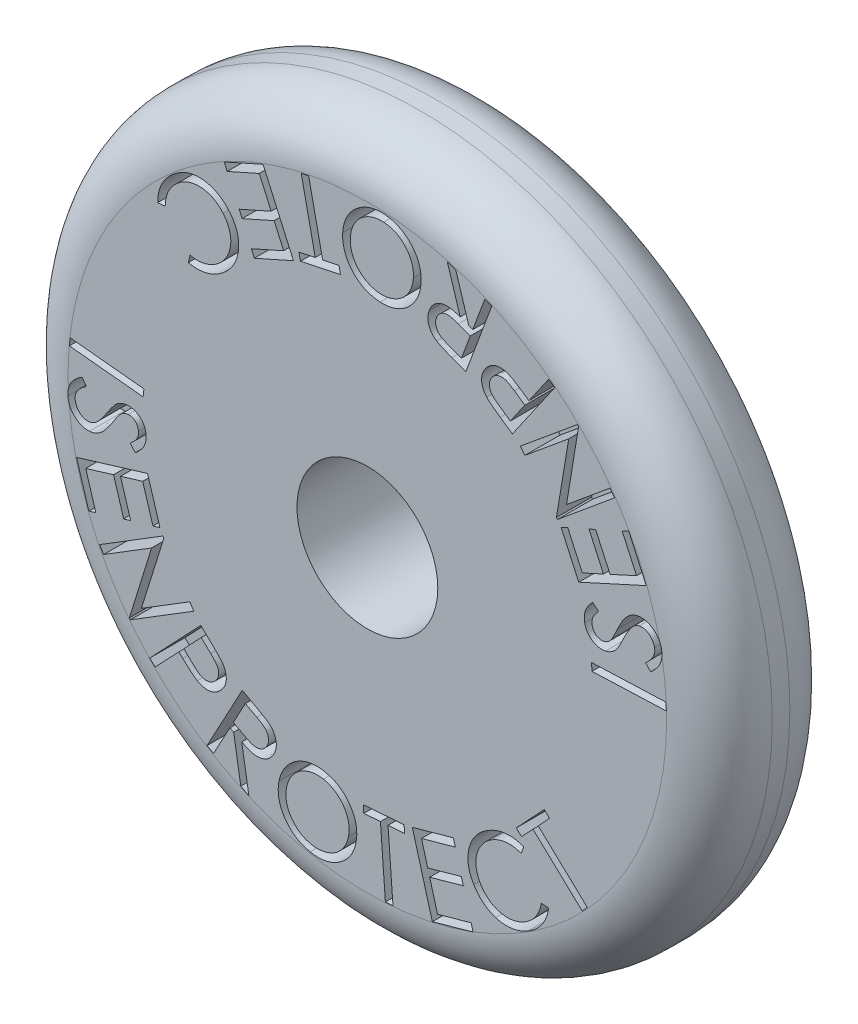
SolidWorks part; units mm, degrees
ref_plane "Plan de face" through (0, 0, 0) normal (0, 0, 1) x (1, 0, 0)
ref_plane "Plan de dessus" through (0, 0, 0) normal (0, 1, 0) x (1, 0, 0)
ref_plane "Plan de droite" through (0, 0, 0) normal (1, 0, 0) x (0, 0, -1)
sketch "Sketch1" plane through (0, 0, 0) normal (0, 0, 1) x (1, 0, 0)
  circle A0 centre (0, 0) radius 20
  dimension "D1" = 40
extrude "Boss-Extrude1" add sketch "Sketch1" along normal blind 7
sketch "Sketch2" plane through (0, 0, 7) normal (0, 0, 1) x (1, 0, 0)
  circle A0 centre (0, 0) radius 4
  dimension "D1" = 8
extrude "Cut-Extrude1" cut sketch "Sketch2" against normal through all
fillet "Fillet1" radius 3 2 edges at (20, 0, 0) (20, 0, 7)
sketch "Sketch4" plane through (0, 0, 7) normal (0, 0, 1) x (1, 0, 0)
  text T0 "ISENPROTEC    ISENPROTECT" font "Century Gothic" height in points 16
extrude "Cut-Extrude3" cut sketch "Sketch4" against normal blind 2
